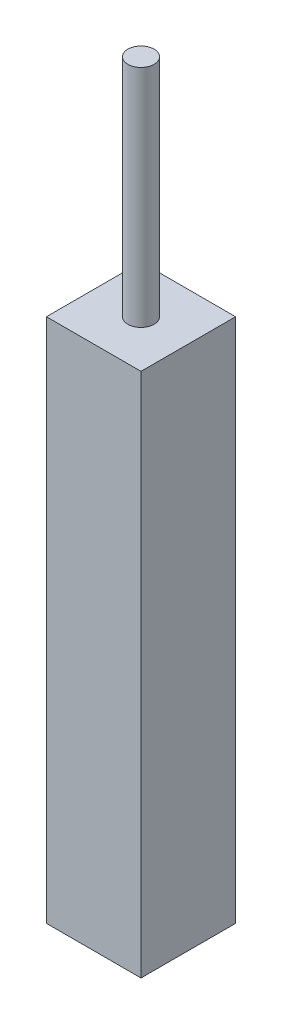
SolidWorks part; units mm, degrees
ref_plane "Front Plane" through (0, 0, 0) normal (0, 0, 1) x (1, 0, 0)
ref_plane "Top Plane" through (0, 0, 0) normal (0, 1, 0) x (1, 0, 0)
ref_plane "Right Plane" through (0, 0, 0) normal (1, 0, 0) x (0, 0, -1)
sketch "Sketch2" plane through (0, 0, 0) normal (0, 1, 0) x (1, 0, 0)
  line L1 (0, 0) -> (2.52, 0)
  line L2 (0, 0) -> (0, 2.52)
  line L3 (0, 2.52) -> (2.52, 2.52)
  line L4 (2.52, 0) -> (2.52, 2.52)
  dimension "D1" = 2.52
extrude "Boss-Extrude1" add sketch "Sketch2" along normal blind 14
sketch "Sketch3" plane through (0, 14, 0) normal (0, 1, 0) x (1, 0, 0)
  line L1 (2.52, 2.52) -> (0, 2.52) construction
  line L2 (2.52, 0) -> (2.52, 2.52) construction
  circle A1 centre (1.26, 1.26) radius 0.35
  point P2 (0, 0)
  point P5 (1.26, 2.52)
  point P8 (2.52, 1.26)
  dimension "D1" = 0.7
extrude "Boss-Extrude2" add sketch "Sketch3" along normal blind 6
